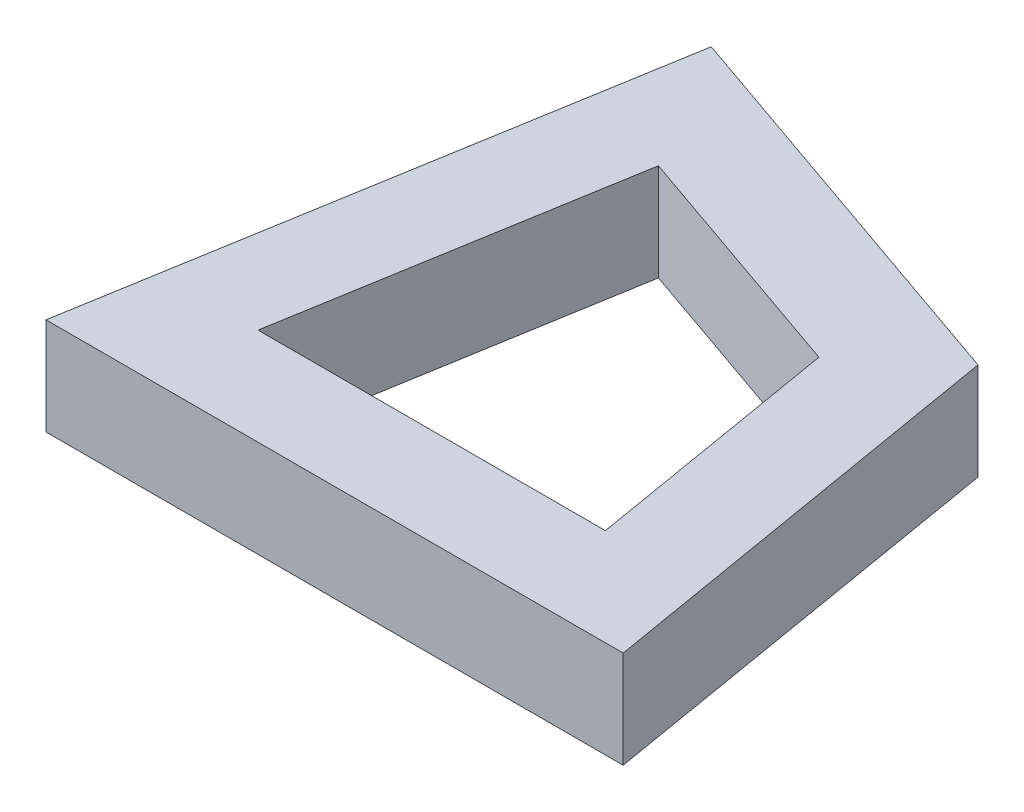
SolidWorks part; units mm, degrees
ref_plane "Front Plane" through (0, 0, 0) normal (0, 0, 1) x (1, 0, 0)
ref_plane "Top Plane" through (0, 0, 0) normal (0, 1, 0) x (1, 0, 0)
ref_plane "Right Plane" through (0, 0, 0) normal (1, 0, 0) x (0, 0, -1)
sketch "Sketch1" plane through (0, 0, 0) normal (0, 1, 0) x (1, 0, 0)
  line L0 (0, 0) -> (11.8844, 0)
  line L1 (11.8844, 0) -> (10.399, 8.7916)
  line L2 (10.399, 8.7916) -> (1.9799, 11.7183)
  line L3 (1.9799, 11.7183) -> (0, 0)
  line L4 (3.5578, 9.0524) -> (2.3663, 2)
  line L5 (2.3663, 2) -> (9.5182, 2)
  line L6 (9.5182, 2) -> (8.6242, 7.2912)
  line L7 (8.6242, 7.2912) -> (3.5578, 9.0524)
  point P4 (0, 0)
  point P10 (35.273, 13.2401)
  point P11 (27.7587, 61.9651)
  point P12 (35.2745, 13.2436)
  point P13 (30.6569, 10.5612)
  point P14 (35.2745, 13.2436)
  point P15 (32.8598, 27.5353)
  dimension "D1" = 11.8844
  dimension "D2" = 80.421
  dimension "D3" = 80.41
  dimension "D4" = 80.41
  dimension "D6" = 8.9162
  dimension "D7" = 8.9133
  dimension "D8" = 11.8844
  dimension "D5" = 2
extrude "Boss-Extrude1" add sketch "Sketch1" along normal blind 2
